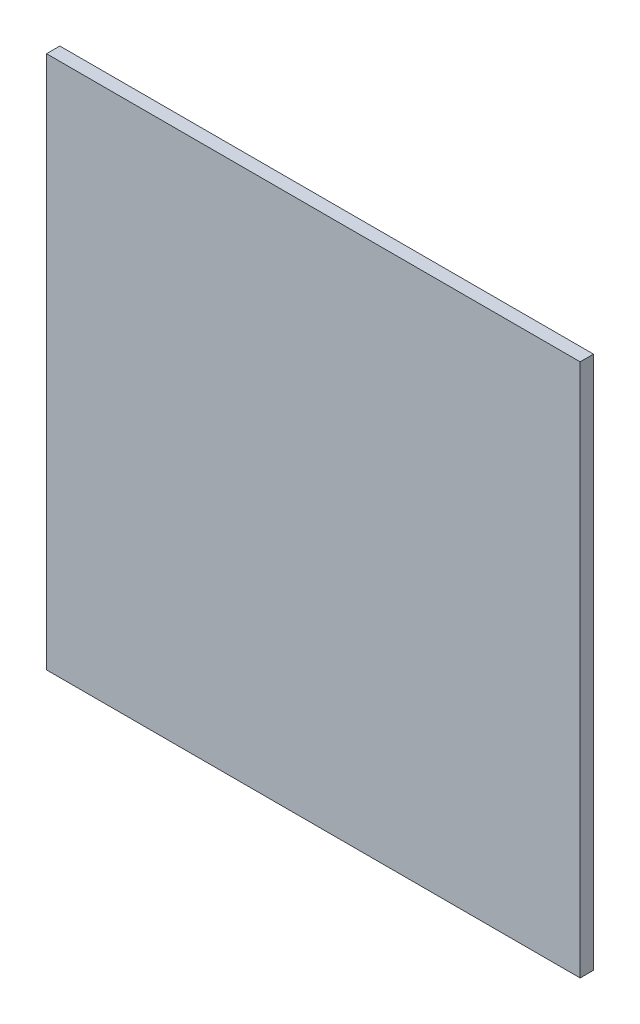
SolidWorks part; units mm, degrees
material "Pinho"
ref_plane "Plano frontal" through (0, 0, 0) normal (0, 0, 1) x (1, 0, 0)
ref_plane "Plano superior" through (0, 0, 0) normal (0, 1, 0) x (1, 0, 0)
ref_plane "Plano direito" through (0, 0, 0) normal (1, 0, 0) x (0, 0, -1)
sketch "Esboço1" plane through (0, 0, 0) normal (0, 0, 1) x (1, 0, 0)
  line L1 (-81.3088, 12.9223) -> (318.6912, 12.9223)
  line L2 (-81.3088, 12.9223) -> (-81.3088, -387.0777)
  line L3 (-81.3088, -387.0777) -> (318.6912, -387.0777)
  line L4 (318.6912, 12.9223) -> (318.6912, -387.0777)
  dimension "D1" = 400
  dimension "D2" = 400
extrude "Ressalto-extrusão1" add sketch "Esboço1" along normal blind 10
